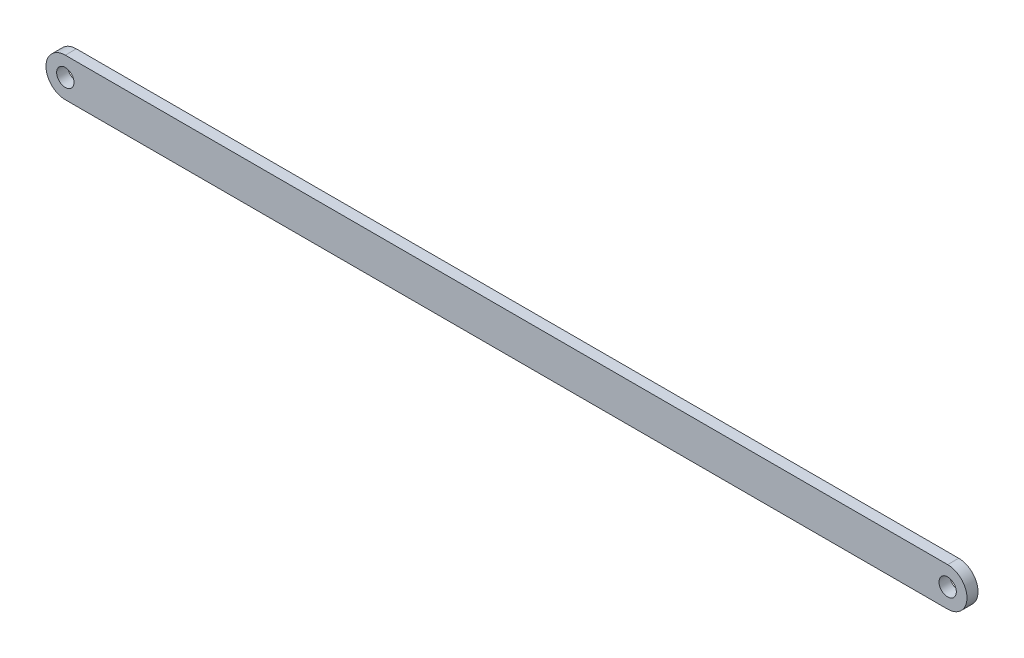
SolidWorks part; units mm, degrees
ref_plane "Front Plane" through (0, 0, 0) normal (0, 0, 1) x (1, 0, 0)
ref_plane "Top Plane" through (0, 0, 0) normal (0, 1, 0) x (1, 0, 0)
ref_plane "Right Plane" through (0, 0, 0) normal (1, 0, 0) x (0, 0, -1)
sketch "Sketch1" plane through (0, 0, 0) normal (0, 0, 1) x (1, 0, 0)
  line L1 (-101.6, 4.445) -> (101.6, 4.445)
  line L2 (-101.6, 4.445) -> (-101.6, -4.445)
  line L3 (-101.6, -4.445) -> (101.6, -4.445)
  line L4 (101.6, 4.445) -> (101.6, -4.445)
  line L5 (-101.6, 4.445) -> (101.6, -4.445) construction
  line L6 (-101.6, -4.445) -> (101.6, 4.445) construction
  circle A0 centre (-101.6, 0) radius 4.445
  circle A1 centre (101.6, 0) radius 4.445
  circle A2 centre (-101.6, 0) radius 1.9939
  circle A3 centre (101.6, 0) radius 1.9939
  point P0 (0, 0)
  point P11 (-101.6, 0)
  point P13 (101.6, 0)
  dimension "D3" = 8.89
  dimension "D4" = 8.89
  dimension "D5" = 3.9878
  dimension "D6" = 3.9878
  dimension "D1" = 8.89
  dimension "D2" = 203.2
extrude "Boss-Extrude1" add sketch "Sketch1" along normal blind 2.54 contours A1 L1 A0 L3 | A2 L2 A0 | A2 L2 A0 | A3 L4 A1 | A3 L4 A1
